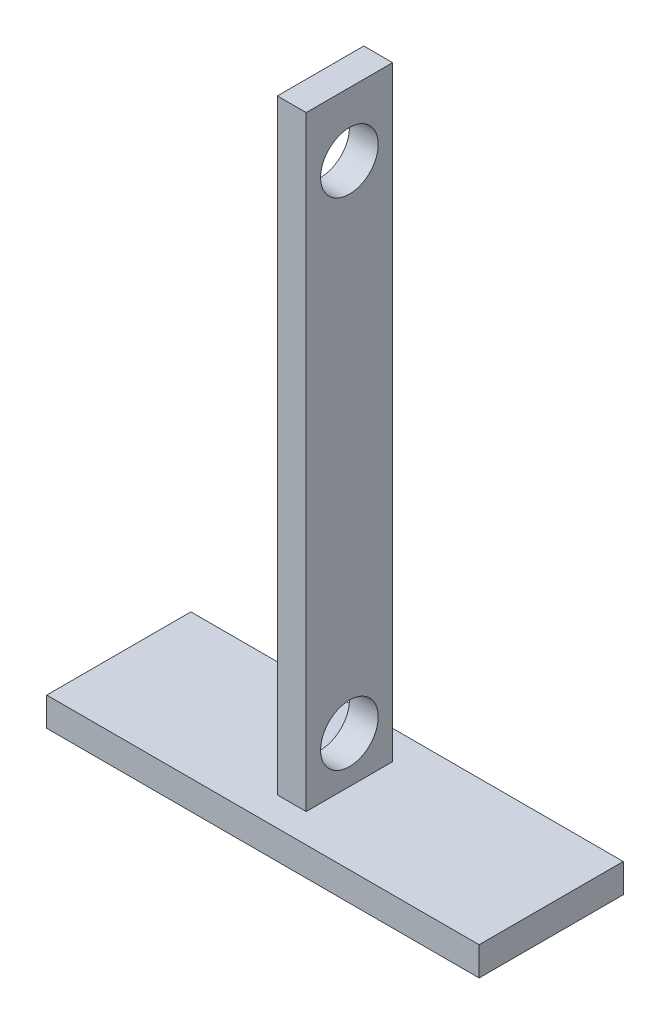
SolidWorks part; units mm, degrees
ref_plane "Front Plane" through (0, 0, 0) normal (0, 0, 1) x (1, 0, 0)
ref_plane "Top Plane" through (0, 0, 0) normal (0, 1, 0) x (1, 0, 0)
ref_plane "Right Plane" through (0, 0, 0) normal (1, 0, 0) x (0, 0, -1)
sketch "Sketch1" plane through (0, 0, 0) normal (0, 1, 0) x (1, 0, 0)
  line L1 (46.8817, 16.25) -> (121.8817, 16.25)
  line L2 (46.8817, 16.25) -> (46.8817, -8.75)
  line L3 (46.8817, -8.75) -> (121.8817, -8.75)
  line L4 (121.8817, 16.25) -> (121.8817, -8.75)
  dimension "D1" = 25
  dimension "D2" = 75
extrude "Boss-Extrude1" add sketch "Sketch1" along normal blind 5
sketch "Sketch2" plane through (0, 5, 0) normal (0, 1, 0) x (1, 0, 0)
  line L0 (46.8817, 3.75) -> (121.8817, 3.75) construction
  line L1 (46.8817, 16.25) -> (46.8817, -8.75) construction
  line L2 (121.8817, -8.75) -> (121.8817, 16.25) construction
  line L4 (86.8817, 11.25) -> (81.8817, 11.25)
  line L5 (86.8817, 11.25) -> (86.8817, -3.75)
  line L6 (86.8817, -3.75) -> (81.8817, -3.75)
  line L7 (81.8817, 11.25) -> (81.8817, -3.75)
  line L8 (86.8817, 11.25) -> (81.8817, -3.75) construction
  line L9 (86.8817, -3.75) -> (81.8817, 11.25) construction
  point P6 (84.3817, 3.75)
  dimension "D1" = 5
  dimension "D2" = 15
extrude "Boss-Extrude3" add sketch "Sketch2" along normal blind 105
sketch "Sketch3" plane through (81.8817, 0, 0) normal (-1, 0, 0) x (0, 0, 1)
  line L0 (-3.75, 110) -> (-3.75, -7.8486) construction
  line L1 (-11.25, 110) -> (3.75, 110) construction
  line L2 (-16.25, 0) -> (8.75, 0) construction
  circle A0 centre (-3.75, 13) radius 5
  dimension "D1" = 13
extrude "Cut-Extrude1" cut sketch "Sketch3" against normal through all
sketch "Sketch4" plane through (81.8817, 0, 0) normal (-1, 0, 0) x (0, 0, 1)
  line L0 (-3.75, 110) -> (-3.75, 27.9524) construction
  line L1 (-11.25, 110) -> (3.75, 110) construction
  circle A0 centre (-3.75, 99) radius 5
  dimension "D1" = 11
extrude "Cut-Extrude2" cut sketch "Sketch4" against normal through all
